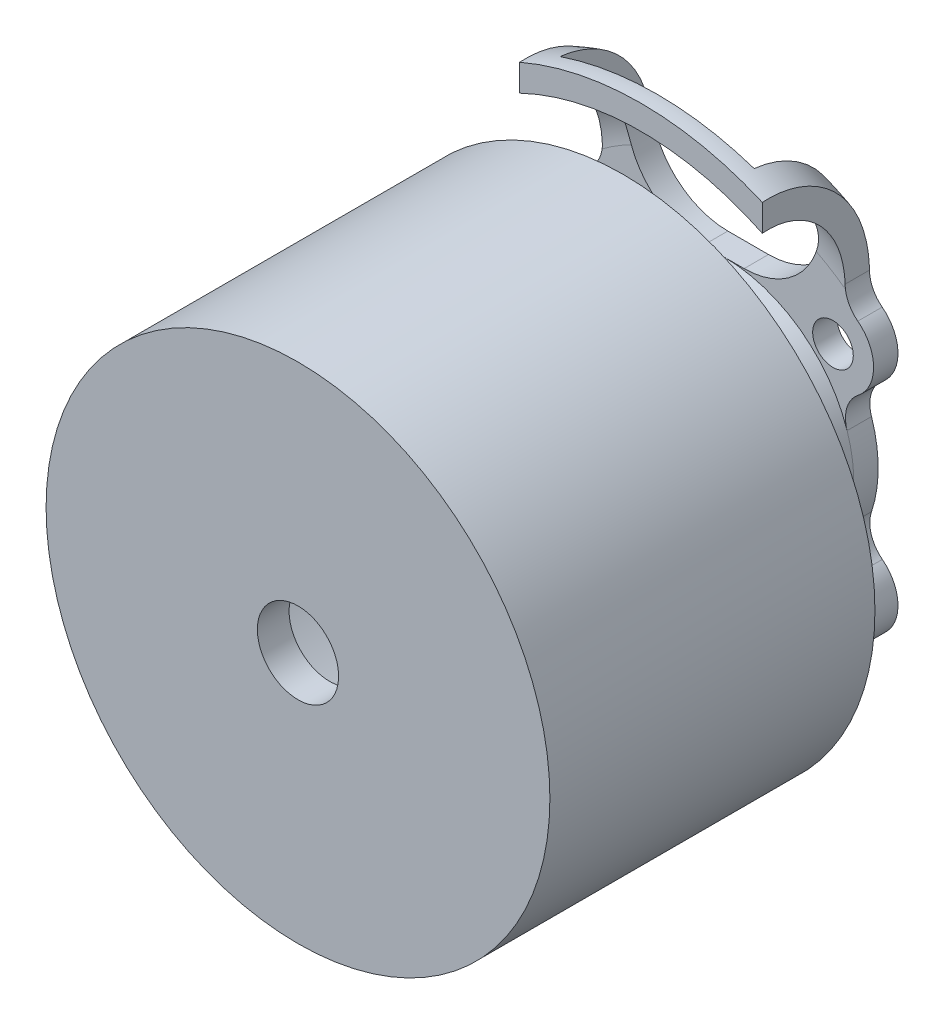
SolidWorks part; units mm, degrees
material "AISI 1020 Steel, Cold Rolled"
ref_plane "Front Plane" through (0, 0, 0) normal (0, 0, 1) x (1, 0, 0)
ref_plane "Top Plane" through (0, 0, 0) normal (0, 1, 0) x (1, 0, 0)
ref_plane "Right Plane" through (0, 0, 0) normal (1, 0, 0) x (0, 0, -1)
sketch "Sketch1" plane through (0, 0, 0) normal (1, 0, 0) x (0, 0, -1)
  line L1 (0, 15.5) -> (20, 15.5)
  line L3 (20, 0) -> (0, 0) construction
  line L4 (20, 2.5) -> (0, 2.5) construction
  line L5 (0, 15.5) -> (0, 2.5)
  line L6 (0, 2.5) -> (1.95, 2.5)
  line L7 (1.95, 2.5) -> (1.95, 13.5)
  line L8 (1.95, 13.5) -> (18.05, 13.5)
  line L9 (18.05, 13.5) -> (18.05, 2.5)
  line L10 (18.05, 2.5) -> (20, 2.5)
  line L11 (20, 6.5) -> (20, 15.5)
  line L12 (20, 2.5) -> (27.7, 2.5)
  line L13 (27.7, 2.5) -> (27.7, 12.5)
  line L14 (27.7, 18.75) -> (-25.5, 18.75) construction
  line L18 (20, 6.5) -> (26.2, 8)
  line L19 (26.2, 8) -> (26.2, 12.5)
  line L20 (21.1007, 18.7402) -> (21.1007, 17.2402)
  line L21 (26.2, 8) -> (27.7, 8) construction
  line L22 (10, 13.5) -> (10, 15.5) construction
  arc A2 (27.7, 12.5) -> (21.1007, 18.7402) centre (21.45, 12.5) ccw
  arc A3 (26.2, 12.5) -> (21.1007, 17.2402) centre (21.4471, 12.5) ccw
  dimension "D10" = 1.5
  dimension "D1" = 20
  dimension "D2" = 15.5
  dimension "D3" = 2.5
  dimension "D4" = 12.5
  dimension "D5" = 27.7
  dimension "D6" = 18.75
  dimension "D7" = 53.2
  dimension "D8" = 6.5
  dimension "D9" = 8
  dimension "D11" = 16.1
  dimension "D12" = 11
revolve "Revolve1" add sketch "Sketch1" angle 360 about L3
sketch "Sketch2" plane through (0, 0, -27.7) normal (0, 0, -1) x (-1, 0, 0)
  line L0 (-5.9675, 23.4161) -> (-5.9675, 12.7175)
  line L1 (-6.7175, -6.7175) -> (6.7175, -6.7175) construction
  line L2 (-6.7175, -6.7175) -> (-6.7175, 6.7175) construction
  line L3 (-6.7175, 6.7175) -> (6.7175, 6.7175) construction
  line L4 (6.7175, -6.7175) -> (6.7175, 6.7175) construction
  line L5 (-6.7175, -6.7175) -> (6.7175, 6.7175) construction
  line L6 (-6.7175, 6.7175) -> (6.7175, -6.7175) construction
  line L7 (-5.9675, 23.4161) -> (5.9675, 23.4161)
  line L8 (5.9675, 23.4161) -> (5.9675, 12.7175)
  line L9 (0, 0) -> (0, 23.4161) construction
  line L10 (1.25, 8) -> (-1.25, 8)
  line L11 (-7.4675, 23.4161) -> (-7.4675, 10.2795)
  line L12 (7.4675, 23.4161) -> (7.4675, 10.2795)
  line L13 (7.4675, 23.4161) -> (5.9675, 23.4161) construction
  line L14 (6.7175, 6.7175) -> (6.7175, 23.4161) construction
  line L15 (-5.9675, 23.4161) -> (-7.4675, 23.4161) construction
  circle A0 centre (0, 0) radius 9.5 construction
  circle A1 centre (0, 0) radius 8 construction
  circle A2 centre (0, 0) radius 12.5 construction
  circle A3 centre (-6.7175, 6.7175) radius 1.25
  circle A4 centre (6.7175, 6.7175) radius 1.25
  circle A5 centre (6.7175, -6.7175) radius 1.25
  circle A6 centre (-6.7175, -6.7175) radius 1.25
  circle A7 centre (6.7175, 6.7175) radius 2.5 construction
  circle A8 centre (6.7175, -6.7175) radius 2.5 construction
  circle A9 centre (-6.7175, -6.7175) radius 2.5 construction
  circle A11 centre (-6.7175, 6.7175) radius 2.5 construction
  arc A17 (-5.9675, 12.7175) -> (-1.25, 8) centre (-1.25, 12.7175) ccw
  arc A19 (5.9675, 12.7175) -> (1.25, 8) centre (1.25, 12.7175) cw
  arc A22 (-7.4675, 23.4161) -> (7.4675, 23.4161) centre (0, -0.8704) ccw
  arc A25 (8.2453, 8.6964) -> (8.2548, 4.746) centre (6.7175, 6.7175) cw
  arc A26 (7.5877, 2.5351) -> (7.5877, -2.5351) centre (0, 0) cw
  arc A27 (8.2548, -4.746) -> (4.746, -8.2548) centre (6.7175, -6.7175) cw
  arc A28 (2.5351, -7.5877) -> (-2.5351, -7.5877) centre (0, 0) cw
  arc A29 (-4.746, -8.2548) -> (-8.2548, -4.746) centre (-6.7175, -6.7175) cw
  arc A30 (-8.2453, 8.6964) -> (-8.2548, 4.746) centre (-6.7175, 6.7175) ccw
  arc A31 (-7.5877, 2.5351) -> (-7.5877, -2.5351) centre (0, 0) ccw
  arc A32 (-8.2453, 8.6964) -> (-7.4675, 10.2795) centre (-9.4675, 10.2795) ccw
  arc A33 (-7.5877, 2.5351) -> (-8.2548, 4.746) centre (-9.4846, 3.1689) ccw
  arc A34 (-8.2548, -4.746) -> (-7.5877, -2.5351) centre (-9.4846, -3.1689) ccw
  arc A35 (-4.746, -8.2548) -> (-2.5351, -7.5877) centre (-3.1689, -9.4846) cw
  arc A36 (2.5351, -7.5877) -> (4.746, -8.2548) centre (3.1689, -9.4846) cw
  arc A37 (8.2548, -4.746) -> (7.5877, -2.5351) centre (9.4846, -3.1689) cw
  arc A38 (7.5877, 2.5351) -> (8.2548, 4.746) centre (9.4846, 3.1689) cw
  arc A39 (8.2453, 8.6964) -> (7.4675, 10.2795) centre (9.4675, 10.2795) cw
  point P47 (7.4675, 9.1024)
  point P48 (-7.4675, 9.1024)
  point P50 (-7.4675, 9.1024)
  point P53 (-6.7972, 4.2188)
  point P56 (-6.7972, -4.2188)
  point P59 (-4.2188, -6.7972)
  point P62 (4.2188, -6.7972)
  point P65 (6.7972, -4.2188)
  point P68 (6.7972, 4.2188)
  point P71 (7.4675, 9.1024)
  point P72 (3.1689, 8)
  point P73 (0, 0)
  point P74 (-2.7646, 8)
  point P75 (-6.7175, 11.6965)
  point P76 (0, 0)
  point P77 (5.9675, 12.0405)
  point P78 (-5.9675, 11.2932)
  point P79 (0, 0)
  dimension "D1" = 19
  dimension "D2" = 16
  dimension "D3" = 25
  dimension "D4" = 2.5
  dimension "D5" = 5
  dimension "D7" = 2
  dimension "D6" = 1.5
  dimension "D8" = 2.5
extrude "Cut-Extrude1" cut sketch "Sketch2" against normal offset from surface (5.5993 mm away) 1 up to face at (-17.2402, 0, -21.1007)
sketch "Sketch3" plane through (0, 0, -21.1007) normal (0, 0, 1) x (1, 0, 0)
  line L0 (-7.4675, 17.1988) -> (-7.4675, 0) construction
  line L1 (-7.4675, 0) -> (7.4675, 0) construction
  line L2 (7.4675, 0) -> (7.4675, 17.1988) construction
  line L4 (7.4675, 15.503) -> (7.4675, 17.1618) construction
  line L5 (7.4675, 17.1988) -> (7.4675, 15.503)
  line L6 (-7.4675, 17.1988) -> (-7.4675, 15.503)
  arc A0 (7.4675, 17.1988) -> (-7.4675, 17.1988) centre (0, 0) cw
  arc A1 (-7.4675, 15.503) -> (7.4675, 15.503) centre (0, 0) ccw
  arc A2 (5.9675, 16.1398) -> (-5.9675, 16.1398) centre (0, 0) ccw construction
  point P5 (0, 0)
  dimension "D1" = 18.75
extrude "Cut-Extrude2" cut sketch "Sketch3" against normal up to next
